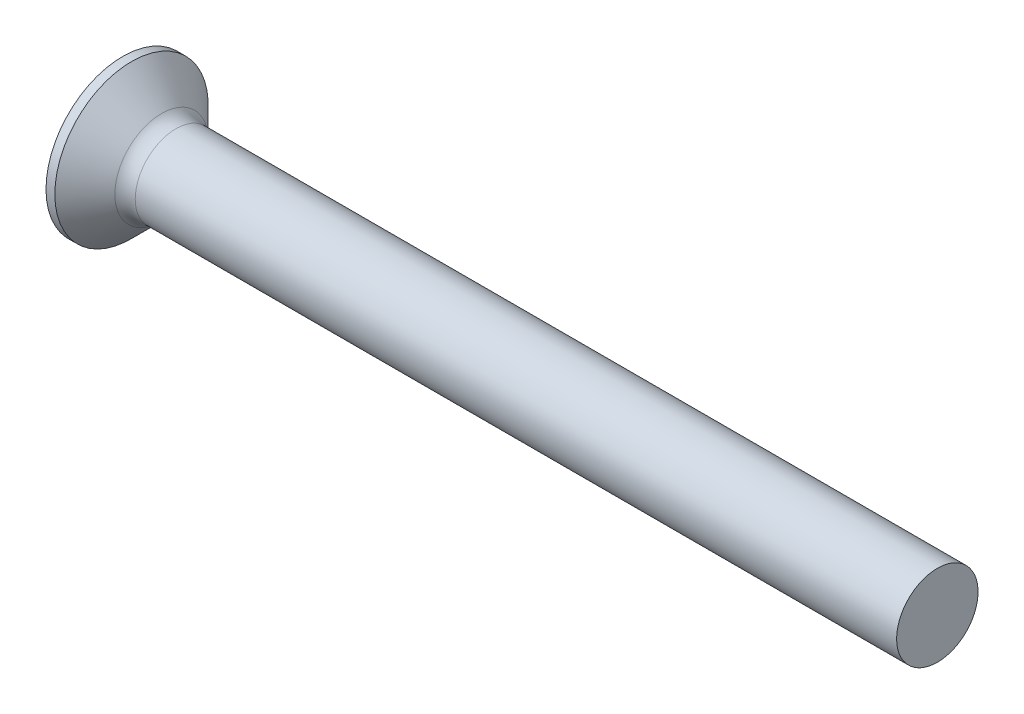
SolidWorks part; units mm, degrees
ref_plane "Plane1" through (0, 0, 0) normal (0, 0, 1) x (1, 0, 0)
ref_plane "Plane2" through (0, 0, 0) normal (0, 1, 0) x (1, 0, 0)
ref_plane "Plane3" through (0, 0, 0) normal (1, 0, 0) x (0, 0, -1)
sketch "BodySke" plane through (0, 0, 0) normal (0, 0, 1) x (1, 0, 0)
  line L0 (0, 0) -> (61.4, 0)
  line L1 (61.4, 0) -> (61.4, 3)
  line L2 (61.4, 3) -> (4.7, 3)
  line L3 (2.05, -5.65) -> (4.7, -3) construction
  line L4 (-15.875, 0) -> (82.55, 0) construction
  line L5 (2.05, 5.65) -> (4.7, 3)
  line L6 (5.7, 6.175) -> (5.7, -9.7) construction
  line L7 (23.4, 2.7793) -> (23.4, -13.0957) construction
  line L8 (2.05, 5.65) -> (1.4, 5.65)
  arc A0 (0, 0) -> (1.4, 5.65) centre (12.1009, 0) cw
  dimension "Head_ang" = 90
  dimension "Diameter" = 6
  dimension "Advance" = 1
  dimension "Thread_nom" = 38
  dimension "Oval_ht" = 1.4
  dimension "Side_ht" = 3.3
  dimension "Head_dia" = 11.3
  dimension "Length" = 60
revolve "Base-Revolve" add sketch "BodySke" angle 360 about L4
cosmetic thread "ThreadCosmetic" [suppressed] parameters "Thread_length"=38, "Thread_minor"=4.891
fillet "Fillet1" radius 1.5 1 edges at (4.7, 0, 3)
sketch "Sketch3" plane through (0, 0, 0) normal (1, 0, 0) x (0, 0, -1)
  line L0 (0.71, -3.55) -> (-0.71, -3.55)
  line L1 (0.71, -3.55) -> (0.71, 3.55)
  line L2 (-0.71, 3.55) -> (0.71, 3.55)
  line L3 (-0.71, 3.55) -> (-0.71, -3.55)
  dimension "Cross_width" = 1.42
  dimension "D1" = 0.71
  dimension "Cross_dia" = 7.1
  dimension "D2" = 3.55
ref_plane "Plane4" through (3.85, 0, 0) normal (1, 0, 0) x (0, 0, -1)
sketch "Sketch4" plane through (3.85, 0, 0) normal (1, 0, 0) x (0, 0, -1)
  line L0 (0.71, -1.6305) -> (-0.71, -1.6305)
  line L1 (0.71, -1.6305) -> (0.71, 1.6305)
  line L2 (-0.71, 1.6305) -> (0.71, 1.6305)
  line L3 (-0.71, 1.6305) -> (-0.71, -1.6305)
  dimension "D1" = 1.42
  dimension "D2" = 3.2609
  dimension "D3" = 0.71
  dimension "D4" = 1.6305
loft "Recess" cut profiles "Sketch3", "Sketch4"
pattern_circular "RecPat" count 2 every 90 about axis through (0, 0, 0) along (1, 0, 0) of "Recess"
sketch "RecCorSke" plane through (0, 0, 0) normal (0, 0, 1) x (1, 0, 0)
  line L0 (-3.175, 0) -> (15.875, 0) construction
  line L2 (0, 0) -> (0, 1.5497)
  line L3 (0, 1.5497) -> (3.85, 1.2805)
  line L4 (3.85, 1.2805) -> (4.2661, 0)
  line L5 (4.2661, 0) -> (0, 0)
  dimension "Diameter" = 2.561
  dimension "Depth" = 3.85
  dimension "Draft_angle" = 4
  dimension "Bottom_angle" = 18
revolve "RecessCore" cut sketch "RecCorSke" angle 360 about L0
sketch "ThdSchSke" plane through (0, 0, 0) normal (0, 0, 1) x (1, 0, 0)
  line L0 (23.4, -2.4455) -> (23.0117, -3)
  line L1 (23.4, -2.4455) -> (23.7883, -3)
  line L2 (23.7883, -3) -> (23.7883, -3.75)
  line L3 (-3.175, 0) -> (5.1513, 0) construction
  line L5 (23.7883, -3.75) -> (23.0117, -3.75)
  line L6 (23.0117, -3.75) -> (23.0117, -3)
  dimension "Diameter" = 6
  dimension "SideAngle" = 55
  dimension "VeeAngle" = 70
  dimension "Thread_minor" = 4.891
  dimension "Overcut" = 7.5
  dimension "Start" = 23.4
revolve "ThreadSchematic" [suppressed] cut sketch "ThdSchSke" angle 360 about L3
pattern_linear "ThdSchPat" [suppressed]
equation "\"D1@Sketch3\" = \"Cross_width@Sketch3\" / 2"
equation "\"D2@Sketch3\" = \"Cross_dia@Sketch3\" / 2"
equation "\"Depth@RecCorSke\" = \"Cross_depth@Plane4\""
equation "\"D1@Sketch4\" = \"Cross_width@Sketch3\""
equation "\"D2@Sketch4\" = \"Cross_dia@Sketch3\" - 2.0 * \"Cross_depth@Plane4\" * tan(26.5  * 0.017453292)"
equation "\"D3@Sketch4\" = \"D1@Sketch4\" / 2"
equation "\"D4@Sketch4\" = \"D2@Sketch4\" / 2"
equation "\"Thread_length@ThreadCosmetic\" = ((sgn( (\"Length@BodySke\" - \"Advance@BodySke\" - \"Side_ht@BodySke\" ) - \"Thread_nom@BodySke\" )-1)*( (\"Length@BodySke\" - \"Advance@BodySke\" - \"Side_ht@BodySke\" ) - \"Thread_nom@BodySke\" ))/-2+ \"Thread_nom@BodySke\""
equation "\"Thread_minor@ThdSchSke\" = \"Thread_minor@ThreadCosmetic\""
equation "\"Diameter@ThdSchSke\" = \"Diameter@BodySke\""
equation "\"Overcut@ThdSchSke\" = \"Diameter@BodySke\" * 1.25"
equation "\"Start@ThdSchSke\" = \"Oval_ht@BodySke\" + \"Length@BodySke\" - \"Thread_length@ThreadCosmetic\"  '---Countersunk---"
equation "\"Num_threads@ThdSchPat\" = int( \"Thread_length@ThreadCosmetic\" / \"Advance@BodySke\" + 0.999 )  + 1"
equation "\"Advance@ThdSchPat\" = \"Thread_length@ThreadCosmetic\" /  (\"Num_threads@ThdSchPat\" - 1) 'relax it"
